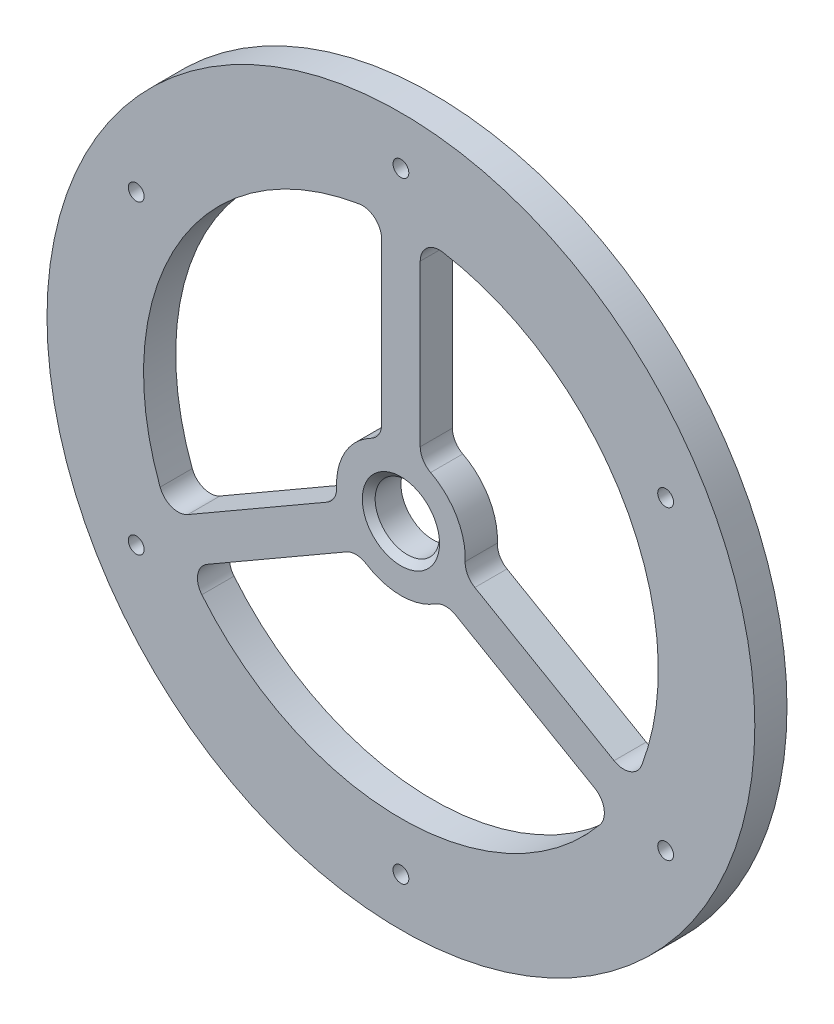
SolidWorks part; units mm, degrees
material "7075-T6 (SN)"
ref_plane "Plan de face" through (0, 0, 0) normal (0, 0, 1) x (1, 0, 0)
ref_plane "Plan de dessus" through (0, 0, 0) normal (0, 1, 0) x (1, 0, 0)
ref_plane "Plan de droite" through (0, 0, 0) normal (1, 0, 0) x (0, 0, -1)
sketch "Esquisse1" plane through (0, 0, 0) normal (0, 0, 1) x (1, 0, 0)
  line L0 (3, 9.5394) -> (3, 39.8873)
  line L1 (-3, 9.5394) -> (-3, 39.8873)
  line L2 (9.7614, -2.1716) -> (36.0435, -17.3456)
  line L3 (6.7614, -7.3678) -> (33.0435, -22.5417)
  line L4 (-6.7614, -7.3678) -> (-33.0435, -22.5417)
  line L5 (-9.7614, -2.1716) -> (-36.0435, -17.3456)
  circle A0 centre (0, 0) radius 55
  arc A1 (-3, 39.8873) -> (-36.0435, -17.3456) centre (0, 0) ccw
  arc A2 (9.7614, -2.1716) -> (3, 9.5394) centre (0, 0) ccw
  circle A3 centre (0, 0) radius 5
  arc A4 (-3, 39.8873) -> (-36.0435, -17.3456) centre (0, 0) ccw
  arc A5 (-3, 39.8873) -> (-36.0435, -17.3456) centre (0, 0) ccw
  arc A6 (-6.7614, -7.3678) -> (6.7614, -7.3678) centre (0, 0) ccw
  arc A7 (-33.0435, -22.5417) -> (33.0435, -22.5417) centre (0, 0) ccw
  arc A8 (-33.0435, -22.5417) -> (33.0435, -22.5417) centre (0, 0) ccw
  arc A9 (-33.0435, -22.5417) -> (33.0435, -22.5417) centre (0, 0) ccw
  arc A10 (36.0435, -17.3456) -> (3, 39.8873) centre (0, 0) ccw
  arc A11 (36.0435, -17.3456) -> (3, 39.8873) centre (0, 0) ccw
  arc A12 (36.0435, -17.3456) -> (3, 39.8873) centre (0, 0) ccw
  arc A13 (-3, 9.5394) -> (-9.7614, -2.1716) centre (0, 0) ccw
  circle A14 centre (0, 0) radius 47.5 construction
  circle A15 centre (0, 47.5) radius 1.227
  circle A16 centre (0, 0) radius 5
  circle A17 centre (41.1362, 23.75) radius 1.227
  circle A18 centre (0, 0) radius 5
  circle A19 centre (41.1362, -23.75) radius 1.227
  circle A20 centre (0, 0) radius 5
  circle A21 centre (0, -47.5) radius 1.227
  circle A22 centre (0, 0) radius 5
  circle A23 centre (-41.1362, -23.75) radius 1.227
  circle A24 centre (0, 0) radius 5
  circle A25 centre (-41.1362, 23.75) radius 1.227
  point P23 (0, 0)
  point P38 (0, 0)
  dimension "D1" = 110
  dimension "D2" = 80
  dimension "D3" = 20
  dimension "D4" = 10
  dimension "D8" = 95
  dimension "D9" = 2.454
  dimension "D5" = 3
  dimension "D6" = 6
  dimension "D7" = 3
  dimension "D10" = 6
extrude "Boss.-Extru.1" add sketch "Esquisse1" along normal blind 5 contours A0 A25 A23 A21 A19 A17 A15 A10 L2 A2 L0 A7 L4 A6 L3 A3 L1 A13 L5 A1
fillet "Congé1" radius 3 12 edges at (-3, 9.5394, 2.5) (-9.7614, -2.1716, 2.5) (3, 9.5394, 2.5) (9.7614, -2.1716, 2.5) (6.7614, -7.3678, 2.5) (-6.7614, -7.3678, 2.5) (-33.0435, -22.5417, 2.5) (-36.0435, -17.3456, 2.5) (-3, 39.8873, 2.5) (3, 39.8873, 2.5) (36.0435, -17.3456, 2.5) (33.0435, -22.5417, 2.5)
chamfer "Chanfrein1" distance 1 angle 45 1 edges at (5, 0, 5)
